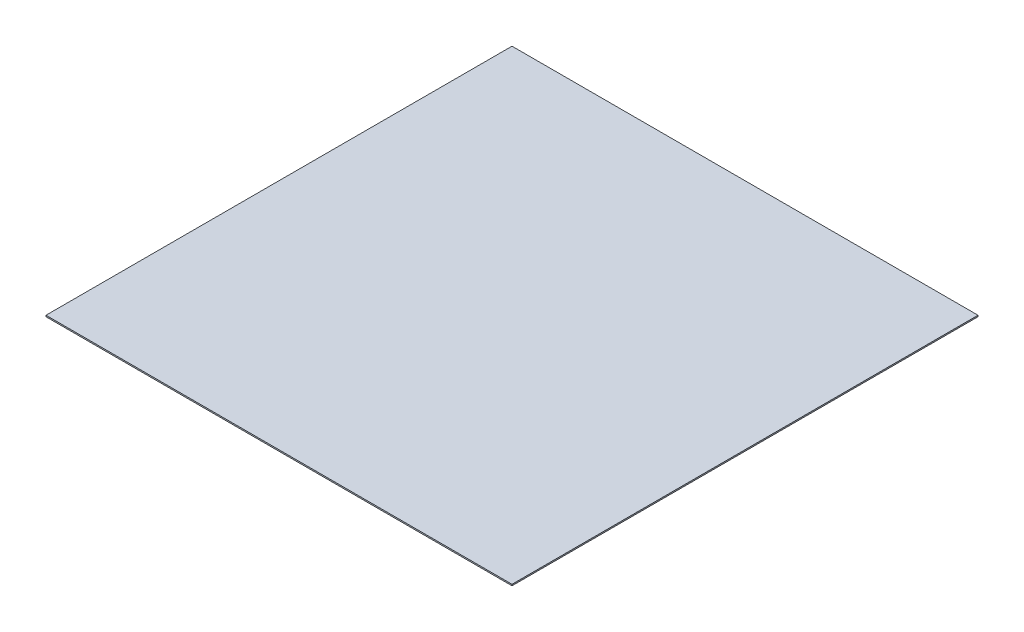
SolidWorks part; units mm, degrees
material "Thornel Mat VMA"
ref_plane "Płaszczyzna przednia" through (0, 0, 0) normal (0, 0, 1) x (1, 0, 0)
ref_plane "Płaszczyzna górna" through (0, 0, 0) normal (0, 1, 0) x (1, 0, 0)
ref_plane "Płaszczyzna prawa" through (0, 0, 0) normal (1, 0, 0) x (0, 0, -1)
sketch "Szkic1" plane through (0, 0, 0) normal (0, 1, 0) x (1, 0, 0)
  line L1 (0, 0) -> (345, 0)
  line L2 (0, 0) -> (0, -345)
  line L3 (0, -345) -> (345, -345)
  line L4 (345, 0) -> (345, -345)
  dimension "D1" = 345
  dimension "D2" = 345
extrude "Dodanie-wyciągnięcie1" add sketch "Szkic1" along normal blind 1
